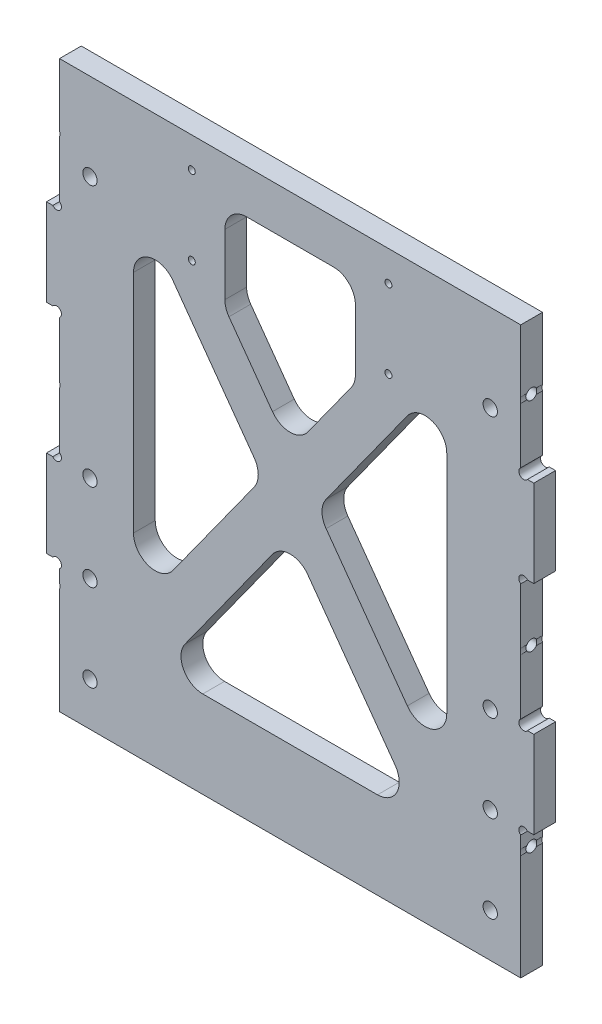
SolidWorks part; units mm, degrees
material "3.1325 (EN-AW 2017A)"
ref_plane "正面" through (0, 0, 0) normal (0, 0, 1) x (1, 0, 0)
ref_plane "平面" through (0, 0, 0) normal (0, 1, 0) x (1, 0, 0)
ref_plane "右側面" through (0, 0, 0) normal (1, 0, 0) x (0, 0, -1)
sketch "ｽｹｯﾁ1" plane through (0, 0, 0) normal (0, 0, 1) x (1, 0, 0)
  line L0 (0, 65) -> (0, -65) construction
  line L1 (-56, -65) -> (56, -65)
  line L2 (-56, -65) -> (-56, 65)
  line L3 (-56, 65) -> (56, 65)
  line L4 (56, -65) -> (56, 65)
  line L5 (-56, -65) -> (56, 65) construction
  line L6 (-56, 65) -> (56, -65) construction
  line L15 (-56, -35) -> (-53, -35)
  line L16 (-56, -35) -> (-56, -65)
  line L17 (-56, -65) -> (-53, -65)
  line L18 (-53, -35) -> (-53, -65) construction
  line L31 (-53, -65) -> (-53, -40.6403)
  line L32 (-53, -39.3597) -> (-53, -35)
  line L33 (-56, 15) -> (-53, 15)
  line L34 (-56, 15) -> (-56, -15)
  line L35 (-56, -15) -> (-53, -15)
  line L38 (-53, 15) -> (-53, 0.6403)
  line L39 (-56, 65) -> (-53, 65)
  line L40 (-56, 65) -> (-56, 35)
  line L41 (-56, 35) -> (-53, 35)
  line L44 (-53, 65) -> (-53, 50.6403)
  line L45 (53, -35) -> (53, -65) construction
  line L46 (53, -39.3597) -> (53, -35)
  line L47 (53, -65) -> (53, -40.6403)
  line L48 (56, -65) -> (53, -65)
  line L49 (56, -35) -> (56, -65)
  line L50 (56, -35) -> (53, -35)
  line L51 (56, 15) -> (56, -15)
  line L52 (56, -15) -> (53, -15)
  line L56 (56, 65) -> (56, 35)
  line L57 (56, 65) -> (53, 65)
  line L61 (56, 15) -> (56, -15)
  line L63 (-53, 9.3597) -> (-53, 15)
  line L64 (-53, -15) -> (-53, 9.3597)
  line L65 (-53, 35) -> (-53, 59.3597)
  line L66 (-53, 60.6403) -> (-53, 65)
  line L67 (-53, 49.3597) -> (-53, 35)
  line L68 (-53, 50.6403) -> (-53, 49.3597) construction
  line L69 (-53, -0.6403) -> (-53, -15)
  line L70 (-53, 0.6403) -> (-53, -0.6403) construction
  line L71 (53, -0.6403) -> (53, -15)
  line L72 (53, 15) -> (53, 0.6403)
  line L73 (56, 15) -> (53, 15)
  line L74 (56, 65) -> (56, 35)
  line L75 (56, 35) -> (53, 35)
  line L76 (53, 49.3597) -> (53, 35)
  line L77 (53, 65) -> (53, 50.6403)
  line L78 (56, 65) -> (53, 65)
  circle A0 centre (-55, -40) radius 2.1 construction
  arc A1 (-53, -39.3597) -> (-53, -40.6403) centre (-55, -40) cw
  arc A3 (-53, 49.3597) -> (-53, 50.6403) centre (-55, 50) ccw
  arc A5 (-53, 50.6403) -> (-56, 51.8466) centre (-55, 50) ccw construction
  circle A6 centre (55, -40) radius 2.1 construction
  arc A7 (53, -39.3597) -> (53, -40.6403) centre (55, -40) ccw
  circle A12 centre (-53.66, -35.66) radius 1.1
  circle A13 centre (53.66, -35.66) radius 1.1
  circle A15 centre (-53.66, -14.34) radius 1.1
  circle A16 centre (-53.66, 14.34) radius 1.1
  circle A17 centre (-53.66, 35.66) radius 1.1
  circle A20 centre (-55, 10) radius 2.1 construction
  arc A21 (-53, 10.6403) -> (-53, 9.3597) centre (-55, 10) cw
  arc A22 (-53, 60.6403) -> (-53, 59.3597) centre (-55, 60) cw
  circle A23 centre (-55, 60) radius 2.1 construction
  arc A24 (-56, 51.8466) -> (-56, 48.1534) centre (-55, 50) ccw construction
  arc A25 (-56, 48.1534) -> (-53, 49.3597) centre (-55, 50) ccw construction
  arc A26 (-53, -0.6403) -> (-53, 0.6403) centre (-55, 0) ccw
  arc A27 (-53, 0.6403) -> (-56, 1.8466) centre (-55, 0) ccw construction
  arc A28 (-56, 1.8466) -> (-56, -1.8466) centre (-55, 0) ccw construction
  arc A29 (-56, -1.8466) -> (-53, -0.6403) centre (-55, 0) ccw construction
  arc A30 (53, -0.6403) -> (53, 0.6403) centre (55, 0) cw
  circle A31 centre (53.66, -14.34) radius 1.1
  circle A32 centre (53.66, 14.34) radius 1.1
  circle A33 centre (53.66, 35.66) radius 1.1
  arc A34 (53, 49.3597) -> (53, 50.6403) centre (55, 50) cw
  point P0 (0, 0)
  point P90 (-56, 0)
  dimension "D10" = 4.2
  dimension "D5" = 2.2
  dimension "D6" = 0.66
  dimension "D8" = 0.66
  dimension "D14" = 0.66
  dimension "D15" = 0.66
  dimension "D16" = 0.66
  dimension "D18" = 0.66
  dimension "D19" = 4.2
  dimension "D21" = 4.2
  dimension "D25" = 2.2
  dimension "D1" = 130
  dimension "D2" = 112
  dimension "D3" = 3
  dimension "D4" = 3
  dimension "D7" = 30
  dimension "D9" = 0.66
  dimension "D11" = 2
  dimension "D12" = 25
  dimension "D20" = 2
  dimension "D22" = 2
  dimension "D23" = 15
  dimension "D13" = 0.66
  dimension "D17" = 0.66
  dimension "D24" = 0.66
extrude "ﾎﾞｽ - 押し出し1" add sketch "ｽｹｯﾁ1" along normal blind 5
sketch "ｽｹｯﾁ2" plane through (-53, 0, 0) normal (-1, 0, 0) x (0, 0, 1)
  line L0 (0, -65) -> (0, -40.6403) construction
  line L1 (5, -65) -> (0, -65) construction
  line L5 (0, 50.6403) -> (0, 49.3597) construction
  circle A0 centre (2.5, -40) radius 1.25
  circle A1 centre (2.5, 0) radius 1.25
  circle A2 centre (2.5, 50) radius 1.25
  point P15 (0, 50)
  dimension "D1" = 2.5
  dimension "D2" = 2.5
  dimension "D3" = 25
extrude "ｶｯﾄ - 押し出し1" cut sketch "ｽｹｯﾁ2" against normal blind 10
mirror "ﾐﾗｰ1" about plane through (0, 0, 0) normal (1, 0, 0) of "ｶｯﾄ - 押し出し1"
sketch "ｽｹｯﾁ3" plane through (0, 0, 5) normal (0, 0, 1) x (1, 0, 0)
  line L0 (-56, -35) -> (-56, -15) construction
  line L1 (-53, -65) -> (53, -65) construction
  line L2 (56, -35) -> (56, -15) construction
  line L3 (-53, 65) -> (53, 65) construction
  circle A0 centre (-46, -55) radius 1.65
  circle A1 centre (46, -55) radius 1.65
  circle A2 centre (46, -35) radius 1.65
  circle A3 centre (-46, -35) radius 1.65
  circle A4 centre (-46, -15) radius 1.65
  circle A5 centre (46, -15) radius 1.65
  circle A6 centre (-46, 45) radius 1.65
  circle A7 centre (46, 45) radius 1.65
  dimension "D1" = 10
  dimension "D2" = 10
  dimension "D3" = 3.3
  dimension "D6" = 20
  dimension "D7" = 10
  dimension "D8" = 10
  dimension "D10" = 20
  dimension "D4" = 2
  dimension "D5" = 3
  dimension "D9" = 2
extrude "ｶｯﾄ - 押し出し2" cut sketch "ｽｹｯﾁ3" against normal blind 10
sketch "ｽｹｯﾁ5" plane through (0, 0, 5) normal (0, 0, 1) x (1, 0, 0)
  circle A0 centre (-22.6, 40) radius 0.8
  circle A1 centre (22.6, 40) radius 0.8
  circle A2 centre (22.6, 58) radius 0.8
  circle A3 centre (-22.6, 58) radius 0.8
  dimension "D1" = 1.6
  dimension "D6" = 45.2
  dimension "D7" = 18
  dimension "D8" = 45.2
  dimension "D2" = 22.6
  dimension "D3" = 40
  dimension "D4" = 2
  dimension "D5" = 2
extrude "ｶｯﾄ - 押し出し4" cut sketch "ｽｹｯﾁ5" against normal blind 10
sketch "ｽｹｯﾁ4" plane through (0, 0, 5) normal (0, 0, 1) x (1, 0, 0)
  line L0 (-15, 55) -> (-15, 34.3905)
  line L1 (-36, 55) -> (36, 55)
  line L2 (-36, 55) -> (-36, -45)
  line L3 (-36, -45) -> (36, -45)
  line L4 (36, 55) -> (36, -45)
  line L5 (-56, 15) -> (-56, 35) construction
  line L7 (-53, -65) -> (53, -65) construction
  line L8 (-53, 65) -> (53, 65) construction
  line L9 (-36, 55) -> (36, -45) construction
  line L10 (-31.9423, 57.9215) -> (40.0577, -42.0785)
  line L11 (-40.0577, 52.0785) -> (31.9423, -47.9215)
  line L12 (-36, -45) -> (36, 55) construction
  line L13 (-40.0577, -42.0785) -> (31.9423, 57.9215)
  line L14 (-31.9423, -47.9215) -> (40.0577, 52.0785)
  line L15 (15, 55) -> (15, 34.3905)
  line L16 (56, 15) -> (56, 35) construction
  arc A1 (-31.9423, 57.9215) -> (-40.0577, 52.0785) centre (-36, 55) ccw
  arc A2 (31.9423, -47.9215) -> (40.0577, -42.0785) centre (36, -45) ccw
  arc A3 (-40.0577, -42.0785) -> (-31.9423, -47.9215) centre (-36, -45) ccw
  arc A4 (40.0577, 52.0785) -> (31.9423, 57.9215) centre (36, 55) ccw
  point P14 (0, 5)
  point P19 (0, 5)
  dimension "D1" = 20
  dimension "D3" = 20
  dimension "D4" = 20
  dimension "D5" = 10
  dimension "D6" = 10
  dimension "D7" = 10
  dimension "D8" = 30
extrude "ｶｯﾄ - 押し出し3" cut sketch "ｽｹｯﾁ4" against normal blind 10 contours L2 L13 L11 | L14 L10 L4 | L14 L3 L11 | L15 L1 L0 L10 L13
fillet "ﾌｨﾚｯﾄ2" radius 5 14 edges at (0, 13.5572, 2.5) (-6.1612, 5, 2.5) (36, -36.4428, 2.5) (29.8388, -45, 2.5) (0, -3.5572, 2.5) (-29.8388, -45, 2.5) (-36, -36.4428, 2.5) (6.1612, 5, 2.5) (36, 46.4428, 2.5) (-36, 46.4428, 2.5) (15, 55, 2.5) (-15, 55, 2.5) (-15, 34.3905, 2.5) (15, 34.3905, 2.5)
